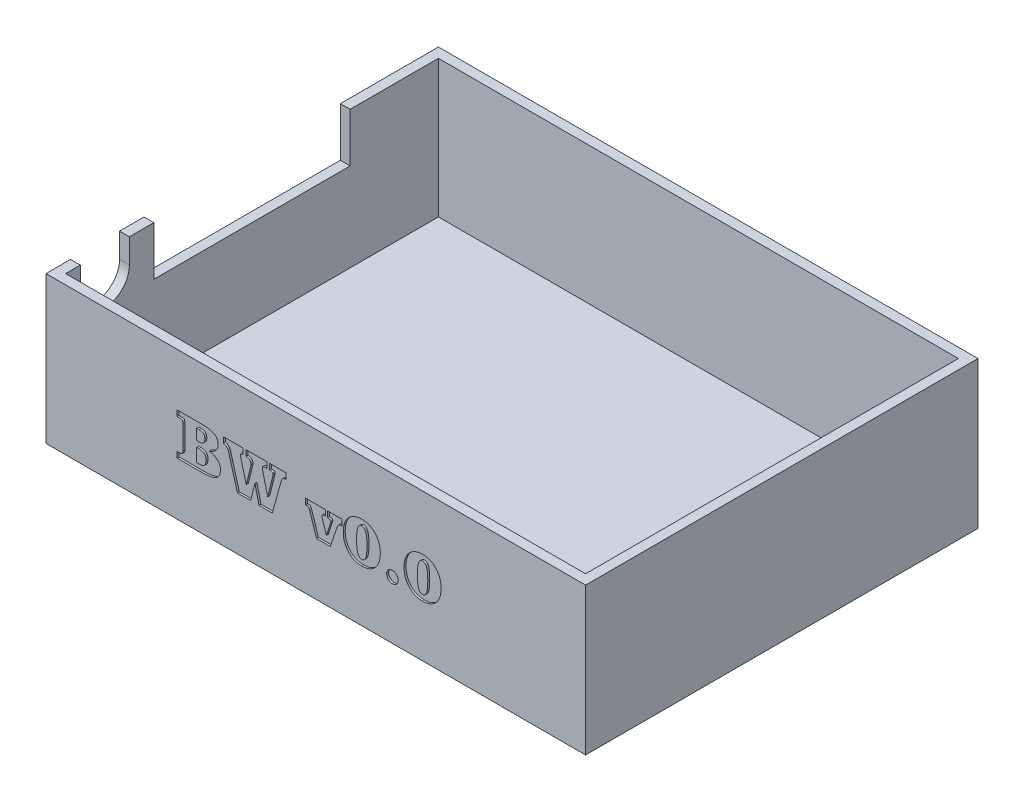
SolidWorks part; units mm, degrees
ref_plane "Front Plane" through (0, 0, 0) normal (0, 0, 1) x (1, 0, 0)
ref_plane "Top Plane" through (0, 0, 0) normal (0, 1, 0) x (1, 0, 0)
ref_plane "Right Plane" through (0, 0, 0) normal (1, 0, 0) x (0, 0, -1)
sketch "Sketch1" plane through (0, 0, 0) normal (0, 1, 0) x (1, 0, 0)
  line L1 (0, 0) -> (110, 0)
  line L2 (0, 0) -> (0, 80)
  line L3 (0, 80) -> (110, 80)
  line L4 (110, 0) -> (110, 80)
extrude "Boss-Extrude1" add sketch "Sketch1" along normal blind 30
shell "Shell1" thickness 2
sketch "Sketch15" plane through (0, 0, 0) normal (-1, 0, 0) x (0, 0, 1)
  line L0 (-40, 30) -> (-40, 0) construction
  line L1 (-80, 30) -> (0, 30) construction
  line L2 (-80, 0) -> (0, 0) construction
  line L4 (-20, 20) -> (-60, 20)
  line L5 (-20, 20) -> (-20, 30)
  line L6 (-20, 30) -> (-60, 30)
  line L7 (-60, 20) -> (-60, 30)
  line L8 (-20, 20) -> (-60, 30) construction
  line L9 (-20, 30) -> (-60, 20) construction
  point P6 (-40, 25)
  dimension "D1" = 40
  dimension "D2" = 10
extrude "Cut-Extrude1" cut sketch "Sketch15" against normal up to next contours L5 L4 L7 L6
sketch "Sketch17" plane through (0, 0, 0) normal (-1, 0, 0) x (0, 0, 1)
  line L0 (-10, 30) -> (-10, 25) construction
  line L1 (-20, 30) -> (0, 30) construction
  line L2 (-80, 0) -> (0, 0) construction
  line L4 (-5, 25) -> (-5, 30)
  line L5 (-15, 25) -> (-15, 30)
  line L6 (-15, 30) -> (-5, 30)
  line L7 (-10, 20) -> (-10, 0) construction
  arc A0 (-15, 25) -> (-5, 25) centre (-10, 25) ccw
extrude "Cut-Extrude2" cut sketch "Sketch17" against normal up to next contours A0 L4 L6 L5
sketch "Sketch19" plane through (0, 0, 0) normal (0, 0, 1) x (1, 0, 0)
  text T0 "BW v0.0" font "Clarendon Blk BT" height 8.5
  point P1 (26.4723, 9.2686)
  point P2 (23.8647, 13.8369)
  point P3 (26.5967, 10.7866)
extrude "Cut-Extrude3" cut sketch "Sketch19" against normal blind 0.4
